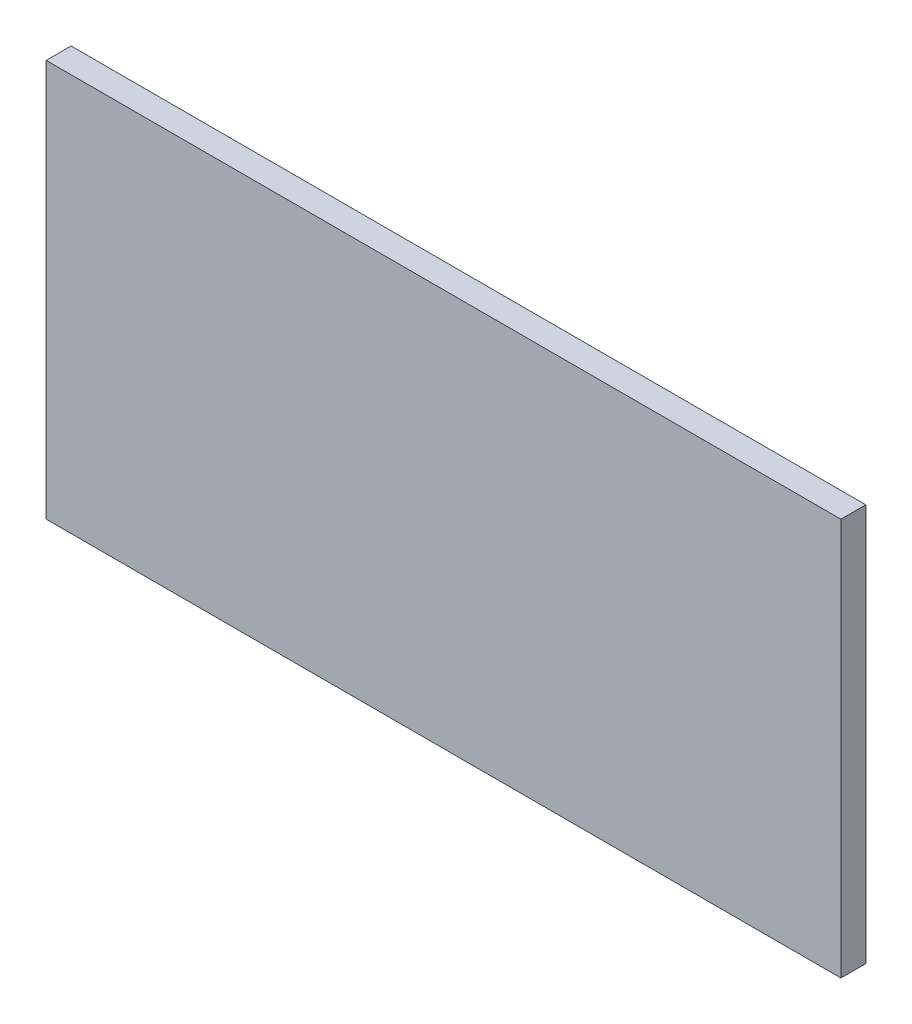
SolidWorks part; units mm, degrees
ref_plane "Front Plane" through (0, 0, 0) normal (0, 0, 1) x (1, 0, 0)
ref_plane "Top Plane" through (0, 0, 0) normal (0, 1, 0) x (1, 0, 0)
ref_plane "Right Plane" through (0, 0, 0) normal (1, 0, 0) x (0, 0, -1)
sketch "Sketch1" plane through (0, 0, 0) normal (0, 0, 1) x (1, 0, 0)
  line L1 (-190.5, -95.25) -> (190.5, -95.25)
  line L2 (-190.5, -95.25) -> (-190.5, 95.25)
  line L3 (-190.5, 95.25) -> (190.5, 95.25)
  line L4 (190.5, -95.25) -> (190.5, 95.25)
  line L5 (-190.5, -95.25) -> (190.5, 95.25) construction
  line L6 (-190.5, 95.25) -> (190.5, -95.25) construction
  point P0 (0, 0)
  dimension "D1" = 381
  dimension "D2" = 190.5
extrude "Boss-Extrude1" add sketch "Sketch1" along normal blind 11.938
